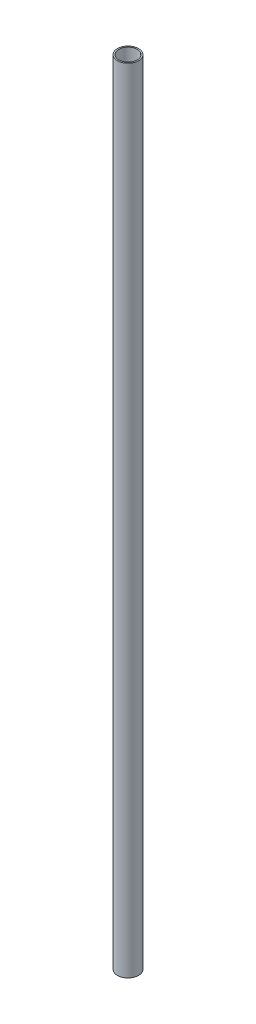
SolidWorks part; units mm, degrees
ref_plane "Front Plane" through (0, 0, 0) normal (0, 0, 1) x (1, 0, 0)
ref_plane "Top Plane" through (0, 0, 0) normal (0, 1, 0) x (1, 0, 0)
ref_plane "Right Plane" through (0, 0, 0) normal (1, 0, 0) x (0, 0, -1)
sketch "Sketch1" plane through (0, 0, 0) normal (0, 1, 0) x (1, 0, 0)
  circle A0 centre (0, 0) radius 4
  circle A1 centre (0, 0) radius 3.5
  dimension "D1" = 8
  dimension "D2" = 7
extrude "Boss-Extrude1" add sketch "Sketch1" along normal blind 300
